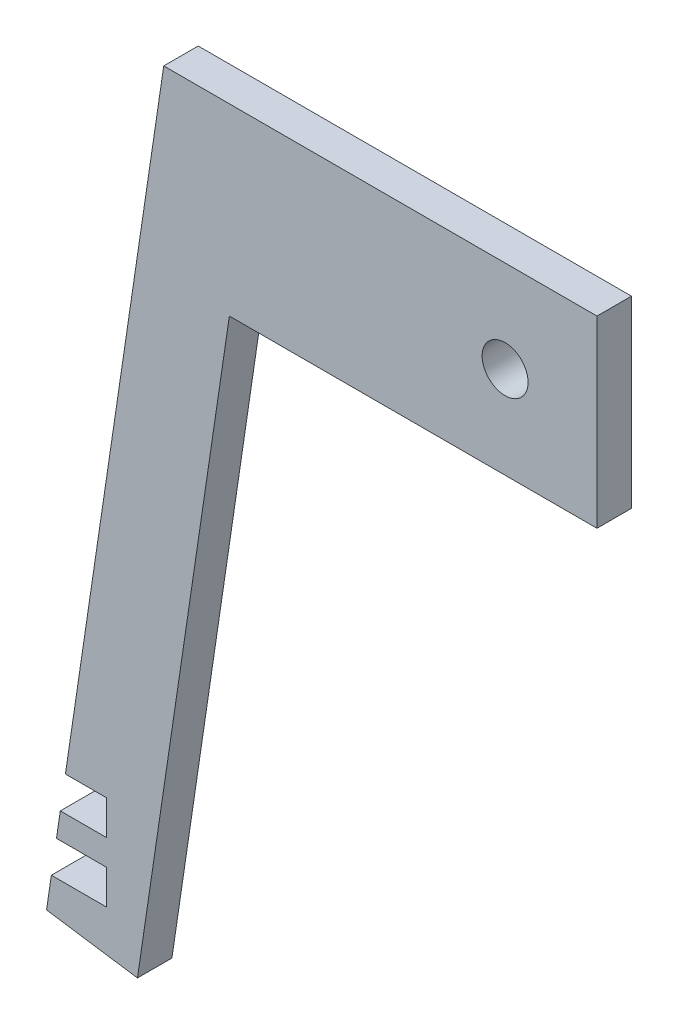
SolidWorks part; units mm, degrees
ref_plane "Front Plane" through (0, 0, 0) normal (0, 0, 1) x (1, 0, 0)
ref_plane "Top Plane" through (0, 0, 0) normal (0, 1, 0) x (1, 0, 0)
ref_plane "Right Plane" through (0, 0, 0) normal (1, 0, 0) x (0, 0, -1)
sketch "Sketch1" plane through (0, 0, 0) normal (0, 0, 1) x (1, 0, 0)
  line L0 (-9.9551, 19.431) -> (3.6308, 110.9668)
  line L3 (0, 0) -> (12.7, 85.5668)
  line L4 (0, 0) -> (-12.5624, 1.8645)
  line L5 (-4.312, 14.6685) -> (-4.312, 19.431)
  line L6 (-4.312, 19.431) -> (-9.9551, 19.431)
  line L7 (-12.5624, 1.8645) -> (-9.9551, 19.431)
  line L8 (-4.312, 14.6685) -> (-10.662, 14.6685)
  line L9 (3.6308, 110.9668) -> (63.5, 110.9668)
  line L10 (-10.662, 14.6685) -> (-11.1898, 11.1125)
  line L11 (63.5, 110.9668) -> (63.5, 85.5668)
  line L12 (63.5, 85.5668) -> (12.7, 85.5668)
  line L13 (-11.1898, 11.1125) -> (-4.312, 11.1125)
  line L14 (-4.312, 6.35) -> (-4.312, 11.1125)
  line L15 (-4.312, 6.35) -> (-11.8966, 6.35)
  circle A0 centre (50.8, 98.2668) radius 3.175
  point P4 (50.8, 98.2668)
  point P5 (0, 0)
  point P17 (0, 0)
  point P18 (0, 0)
  dimension "D11" = 6.35
  dimension "D2" = 4.7625
  dimension "D3" = 6.35
  dimension "D4" = 4.7625
  dimension "D5" = 25.4
  dimension "D7" = 12.7
  dimension "D8" = 50.8
  dimension "D9" = 12.7
  dimension "D10" = 12.7
  dimension "D12" = 98.2668
  dimension "D13" = 6.35
  dimension "D14" = 3.556
  dimension "D15" = 50.8
extrude "Boss-Extrude1" add sketch "Sketch1" along normal blind 4.7625
